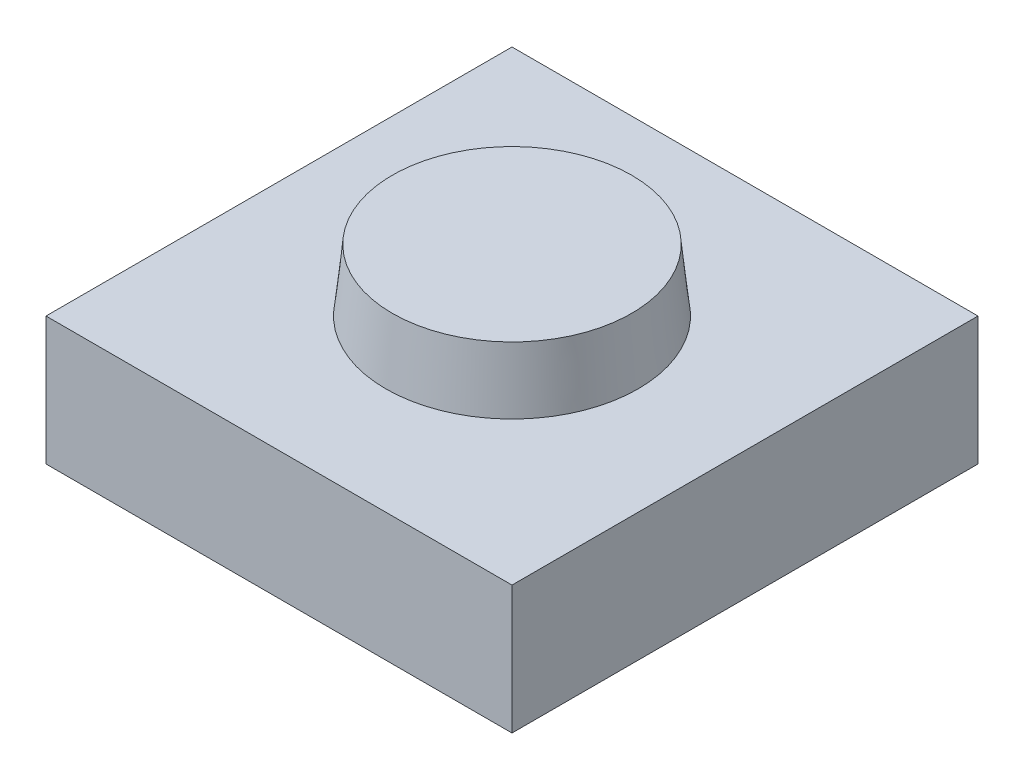
SolidWorks part; units mm, degrees
ref_plane "Спереди" through (0, 0, 0) normal (0, 0, 1) x (1, 0, 0)
ref_plane "Сверху" through (0, 0, 0) normal (0, 1, 0) x (1, 0, 0)
ref_plane "Справа" through (0, 0, 0) normal (1, 0, 0) x (0, 0, -1)
sketch "Sketch1" plane through (0, 0, 0) normal (0, 1, 0) x (1, 0, 0)
  line L1 (6, -6) -> (-6, -6)
  line L2 (6, -6) -> (6, 6)
  line L3 (6, 6) -> (-6, 6)
  line L4 (-6, -6) -> (-6, 6)
  line L5 (6, -6) -> (-6, 6) construction
  line L6 (6, 6) -> (-6, -6) construction
  point P0 (0, 0)
  dimension "D1" = 12
extrude "Boss-Extrude1" add sketch "Sketch1" along normal blind 3.3
sketch "Sketch2" plane through (0, 3.3, 0) normal (0, 1, 0) x (1, 0, 0)
  line L0 (0, -6) -> (0, 6) construction
  line L1 (-6, -6) -> (6, -6) construction
  line L2 (6, 6) -> (-6, 6) construction
  circle A0 centre (0, 0) radius 3.25
  dimension "D1" = 6.5
extrude "Boss-Extrude2" add sketch "Sketch2" along normal blind 1.6 draft 6
